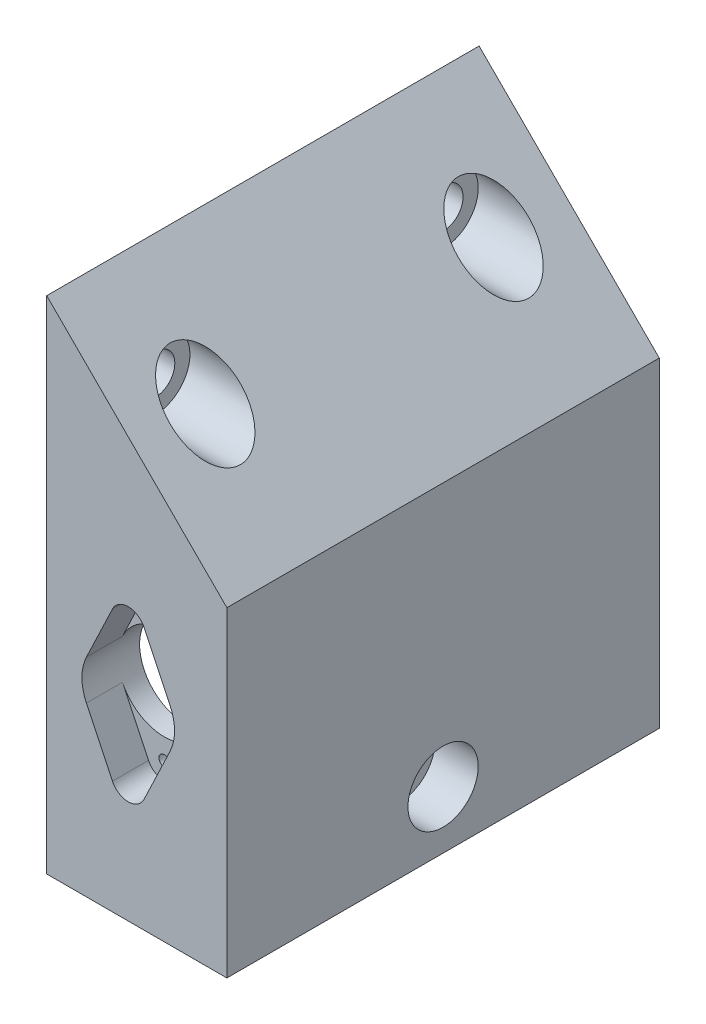
SolidWorks part; units mm, degrees
ref_plane "Front Plane" through (0, 0, 0) normal (0, 0, 1) x (1, 0, 0)
ref_plane "Top Plane" through (0, 0, 0) normal (0, 1, 0) x (1, 0, 0)
ref_plane "Right Plane" through (0, 0, 0) normal (1, 0, 0) x (0, 0, -1)
sketch "Sketch1" plane through (0, 0, 0) normal (0, 0, 1) x (1, 0, 0)
  line L0 (0.4849, 27.1716) -> (0.4849, 30)
  line L1 (0.4849, -37.5) -> (0.4849, -39.5)
  line L2 (4.8853, -0.1423) -> (18.3853, -0.1423)
  line L3 (0.4849, 30) -> (0.4849, -37.5)
  line L6 (4.8853, -29.1423) -> (18.3853, -29.1423)
  line L7943 (25.4849, -39.5) -> (0.4849, -39.5)
  line L8278 (25.4849, 5) -> (0.4849, 30)
  line L8280 (25.4849, 5) -> (25.4849, -39.5)
  line L8281 (23.4849, 4.1716) -> (0.4849, 27.1716)
  line L8282 (23.4849, 4.1716) -> (23.4849, -37.5)
  line L8283 (23.4849, -37.5) -> (0.4849, -37.5)
  line L8307 (18.3853, -0.1423) -> (18.3853, -29.1423)
  line L8309 (4.8853, -0.1423) -> (4.8853, -29.1423)
  point P11661 (-16.5151, -30)
  dimension "D1" = 29
extrude "Boss-Extrude1" add sketch "Sketch1" along normal blind 2
sketch "Sketch2" plane through (0, 0, 2) normal (0, 0, 1) x (1, 0, 0)
  line L0 (0.4849, -37.5) -> (0.4849, -39.5) construction
  line L1 (25.4849, -39.5) -> (0.4849, -39.5) construction
  line L2 (25.4849, 5) -> (25.4849, -39.5) construction
  line L3 (25.4849, 5) -> (0.4849, 30) construction
  line L4 (0.4849, 30) -> (0.4849, -37.5) construction
  line L5 (0.4849, 27.1716) -> (0.4849, 30) construction
  line L6 (23.4849, 4.1716) -> (0.4849, 27.1716) construction
  line L7 (23.4849, 4.1716) -> (23.4849, -37.5) construction
  line L8 (23.4849, -37.5) -> (0.4849, -37.5) construction
  line L10 (18.3853, -0.1423) -> (18.3853, -29.1423) construction
  line L12 (4.8853, -0.1423) -> (4.8853, -29.1423) construction
  line L13 (0.4849, -37.5) -> (0.4849, -39.5)
  line L14 (25.4849, -39.5) -> (0.4849, -39.5)
  line L15 (25.4849, 5) -> (25.4849, -39.5)
  line L16 (25.4849, 5) -> (0.4849, 30)
  line L17 (0.4849, 30) -> (0.4849, -37.5)
  line L18 (0.4849, 27.1716) -> (0.4849, 30)
  line L19 (23.4849, 4.1716) -> (0.4849, 27.1716)
  line L20 (23.4849, 4.1716) -> (23.4849, -37.5)
  line L21 (23.4849, -37.5) -> (0.4849, -37.5)
  line L22 (4.8853, -0.1423) -> (18.3853, -0.1423)
  line L23 (18.3853, -0.1423) -> (18.3853, -29.1423)
  line L24 (4.8853, -29.1423) -> (18.3853, -29.1423)
  line L25 (4.8853, -0.1423) -> (4.8853, -29.1423)
  line M1 (0.4849, 30) -> (0.4849, -39.5)
  line M2 (0.4849, -39.5) -> (25.4849, -39.5)
  line M3 (25.4849, -39.5) -> (25.4849, 5)
  line M4 (25.4849, 5) -> (0.4849, 30)
extrude "Boss-Extrude2" add sketch "Sketch2" along normal blind 56 contours L20 L21 L19 M1 M2 M3 M4
sketch "Sketch3" plane through (0, 0, 58) normal (0, 0, 1) x (1, 0, 0)
  line L0 (0.4849, 30) -> (0.4849, -39.5)
  line L1 (0.4849, -39.5) -> (25.4849, -39.5)
  line L2 (0.4849, -39.5) -> (25.4849, -39.5) construction
  line L3 (25.4849, -39.5) -> (25.4849, 5)
  line L4 (25.4849, 5) -> (0.4849, 30)
  line L6 (22.1819, -8.8838) -> (1.1819, -8.8838) construction
extrude "Boss-Extrude3" add sketch "Sketch3" along normal blind 2
sketch "Sketch5" plane through (25.4849, 0, 0) normal (1, 0, 0) x (0, 0, -1)
  line L0 (-60, -39.5) -> (0, -39.5)
  line L1 (-60, -39.5) -> (0, -39.5) construction
  line L2 (-60, -39.5) -> (-60, 5) construction
  circle A0 centre (-30, -31.5) radius 4.75
  circle A1 centre (-30, -31.5) radius 2.775
  circle A2 centre (-30, -31.5) radius 4.75
  dimension "D1" = 8
sketch "Sketch6" plane through (23.4849, 0, 0) normal (-1, 0, 0) x (0, 0, 1)
  line L1 (37, -31.5) -> (37, -37.5)
  line L2 (58, -37.5) -> (2, -37.5) construction
  line L3 (23, -31.5) -> (23, -37.5)
  line L4 (23, -37.5) -> (37, -37.5)
  line L7 (58, -37.5) -> (58, 4.1716)
  line L8 (58, 4.1716) -> (2, 4.1716)
  line L9 (2, 4.1716) -> (2, -37.5)
  line L10 (2, -37.5) -> (58, -37.5)
  line L11 (58, -37.5) -> (58, 4.1716)
  line L12 (58, 4.1716) -> (2, 4.1716)
  line L13 (2, 4.1716) -> (2, -37.5)
  arc A0 (37, -31.5) -> (23, -31.5) centre (30, -31.5) ccw
  dimension "D2" = 7
  dimension "D1" = 0
extrude "Boss-Extrude6" add sketch "Sketch6" along normal up to surface (23 mm away) up to face at (0.4849, -4.75, 30)
sketch "Sketch7" plane through (25.4849, 0, 0) normal (1, 0, 0) x (0, 0, -1)
  circle A0 centre (-30, -31.5) radius 4.875
extrude "Cut-Extrude2" cut sketch "Sketch7" against normal blind 6
sketch "Sketch8" plane through (25.4849, 0, 0) normal (1, 0, 0) x (0, 0, -1)
  line L0 (-60, -39.5) -> (-60, 30)
  line L1 (-60, 30) -> (0, 30)
  line L2 (0, 30) -> (0, -39.5)
  line L3 (0, -39.5) -> (-60, -39.5)
  line L8 (-30, 30) -> (-30, -39.5) construction
  circle A0 centre (-50, 18) radius 2.775
  circle A1 centre (-50, 18) radius 4.875
  circle A2 centre (-10, 18) radius 4.875
  circle A3 centre (-10, 18) radius 2.775
  dimension "D1" = 9.75
  dimension "D2" = 20
  dimension "D3" = 12
sketch "Sketch9" plane through (0, 0, 2) normal (0, 0, 1) x (1, 0, 0)
  line L0 (0.4849, 27.1716) -> (17.5418, 10.1147)
  line L1 (23.4849, 4.1716) -> (0.4849, 27.1716) construction
  line L2 (17.5418, 10.1147) -> (0.4849, 10.1147)
  line L3 (0.4849, 27.1716) -> (0.4849, -37.5) construction
  line L4 (0.4849, 10.1147) -> (0.4849, 27.1716)
extrude "Boss-Extrude7" add sketch "Sketch9" along normal up to next
sketch "Sketch14" plane through (0, 0, 58) normal (0, 0, -1) x (-1, 0, 0)
  line L0 (-17.5418, 10.1147) -> (-0.4849, 10.1147)
  line L1 (-0.4849, 10.1147) -> (-0.4849, -37.5)
  line L2 (-0.4849, -37.5) -> (-23.4849, -37.5)
  line L3 (-23.4849, -37.5) -> (-23.4849, 4.1716)
  line L4 (-23.4849, 4.1716) -> (-17.5418, 10.1147)
extrude "Boss-Extrude8" add sketch "Sketch14" along normal blind 6
sketch "Sketch15" plane through (0, 0, 60) normal (0, 0, 1) x (1, 0, 0)
  line L8 (9.6068, -3.1) -> (5.9957, -10.6796)
  line L9 (5.9957, -16.2065) -> (9.6068, -23.786)
  line L10 (13.9853, -23.786) -> (17.5964, -16.2065)
  line L11 (13.9853, -3.1) -> (17.5964, -10.6796)
  arc A4 (5.9957, -10.6796) -> (5.9957, -16.2065) centre (11.796, -13.443) ccw
  arc A5 (9.6068, -23.786) -> (13.9853, -23.786) centre (11.796, -22.743) ccw
  arc A6 (17.5964, -16.2065) -> (17.5964, -10.6796) centre (11.796, -13.443) ccw
  arc A7 (13.9853, -3.1) -> (9.6068, -3.1) centre (11.796, -4.143) ccw
extrude "Cut-Extrude11" cut sketch "Sketch15" against normal blind 5
sketch "Sketch17" plane through (0, 0, 55) normal (0, 0, 1) x (1, 0, 0)
  circle A0 centre (11.796, -4.143) radius 0.75
  circle A1 centre (11.796, -22.743) radius 0.75
extrude "Cut-Extrude13" cut sketch "Sketch17" against normal blind 6
sketch "Sketch18" plane through (0, 0, 55) normal (0, 0, 1) x (1, 0, 0)
  circle A0 centre (11.796, -13.443) radius 6.425
extrude "Cut-Extrude14" cut sketch "Sketch18" against normal blind 6
extrude "Cut-Extrude20" cut sketch "Sketch8" against normal blind 20 contours A1 A0 | A2 A3
extrude "Cut-Extrude21" cut sketch "Sketch5" against normal through all contours A1
sketch "Sketch19" plane through (25.4849, 0, 0) normal (1, 0, 0) x (0, 0, -1)
  circle A0 centre (-50, 18) radius 2.775
  circle A1 centre (-10, 18) radius 2.775
extrude "Cut-Extrude22" cut sketch "Sketch19" against normal through all
